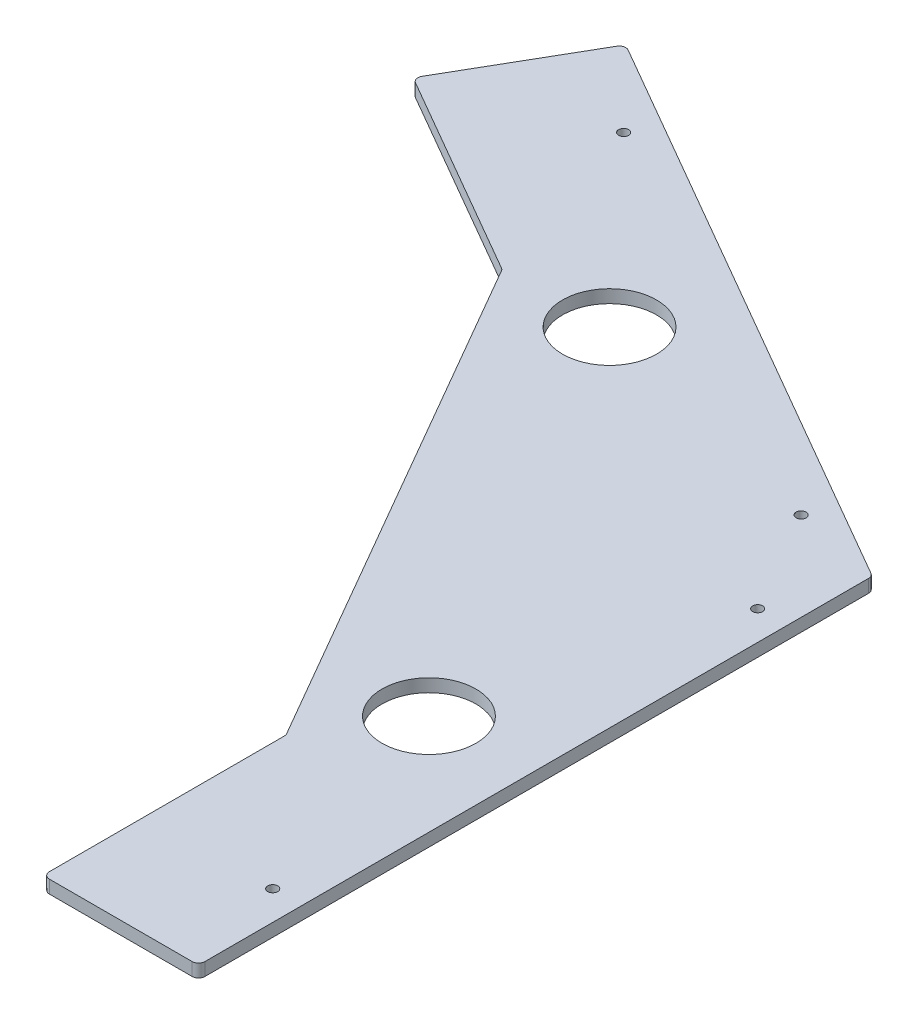
SolidWorks part; units mm, degrees
material "PE High Density"
ref_plane "Front Plane" through (0, 0, 0) normal (0, 0, 1) x (1, 0, 0)
ref_plane "Top Plane" through (0, 0, 0) normal (0, 1, 0) x (1, 0, 0)
ref_plane "Right Plane" through (0, 0, 0) normal (1, 0, 0) x (0, 0, -1)
sketch "Sketch1" plane through (0, 0, 0) normal (0, 1, 0) x (1, 0, 0)
  line L0 (0, 0) -> (0, 329.9557)
  line L1 (0, 329.9557) -> (-285.75, 494.9335)
  line L2 (-285.75, 494.9335) -> (-323.85, 428.9424)
  line L4 (-76.2, 0) -> (0, 0)
  line L5 (-249.0661, 457.2562) -> (-43.4069, 338.5189) construction
  line L6 (0, 329.9557) -> (-109.6099, 266.6724) construction
  line L7 (-170.0073, 371.2837) -> (-49.2125, 162.061) construction
  line L8 (-43.4069, 338.5189) -> (-14.2875, 288.0826) construction
  line L9 (-14.2875, 288.0826) -> (-14.2875, 50.6079) construction
  line L10 (-14.2875, 50.6079) -> (-249.0661, 457.2562) construction
  line L11 (-323.85, 428.9424) -> (-220.7601, 369.4234)
  line L12 (-220.7601, 369.4234) -> (-76.2, 119.038)
  line L13 (-76.2, 119.038) -> (-76.2, 0)
  circle A3 centre (-49.2125, 162.061) radius 23.0187
  circle A4 centre (-170.0073, 371.2837) radius 23.0188
  circle A5 centre (-14.2875, 50.6079) radius 2.4574
  circle A6 centre (-14.2875, 288.0826) radius 2.4574
  circle A7 centre (-43.4069, 338.5189) radius 2.4574
  circle A8 centre (-249.0661, 457.2562) radius 2.4575
  point P17 (-109.6099, 266.6724)
  dimension "D6" = 14.2875
  dimension "D8" = 46.0375
  dimension "D4" = 4.9149
  dimension "D1" = 120
  dimension "D2" = 571.5
  dimension "D3" = 76.2
  dimension "D5" = 14.2875
  dimension "D7" = 49.2125
  dimension "D9" = 241.5896
  dimension "D10" = 237.4748
  dimension "D11" = 469.5571
  dimension "D12" = 171.45
extrude "Boss-Extrude1" add sketch "Sketch1" along normal blind 6.35
fillet "Fillet1" radius 3.175 7 edges at (-285.75, 3.175, -494.9335) (0, 3.175, -329.9557) (0, 3.175, 0) (-76.2, 3.175, -119.038) (-220.7601, 3.175, -369.4234) (-323.85, 3.175, -428.9424) (-76.2, 3.175, 0)
